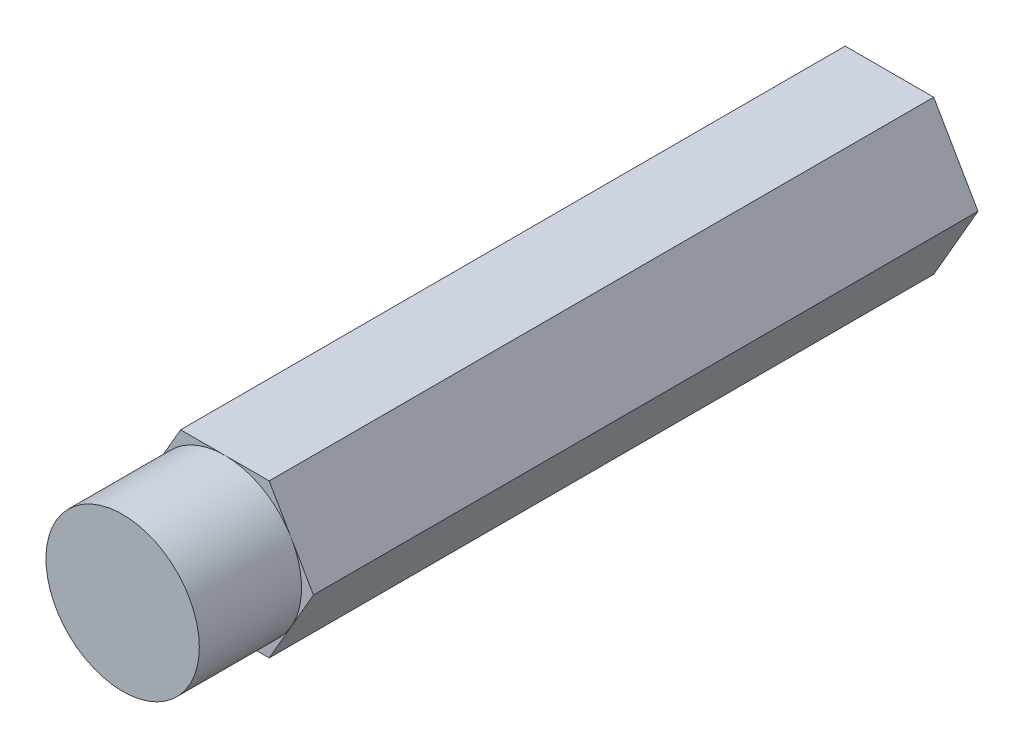
SolidWorks part; units mm, degrees
material "7075-T6 (SN)"
ref_plane "Front Plane" through (0, 0, 0) normal (0, 0, 1) x (1, 0, 0)
ref_plane "Top Plane" through (0, 0, 0) normal (0, 1, 0) x (1, 0, 0)
ref_plane "Right Plane" through (0, 0, 0) normal (1, 0, 0) x (0, 0, -1)
sketch "Sketch1" plane through (0, 0, 0) normal (0, 0, 1) x (1, 0, 0)
  line L1 (-2.7496, -4.7625) -> (2.7496, -4.7625)
  line L2 (2.7496, -4.7625) -> (5.4993, 0)
  line L3 (5.4993, 0) -> (2.7496, 4.7625)
  line L4 (2.7496, 4.7625) -> (-2.7496, 4.7625)
  line L5 (-2.7496, 4.7625) -> (-5.4993, 0)
  line L6 (-5.4993, 0) -> (-2.7496, -4.7625)
  circle A0 centre (0, 0) radius 4.7625 construction
  dimension "D1" = 9.525
extrude "Boss-Extrude1" add sketch "Sketch1" along normal blind 41.275
sketch "Sketch2" plane through (0, 0, 41.275) normal (0, 0, 1) x (1, 0, 0)
  circle A0 centre (0, 0) radius 4.7625
  dimension "D1" = 9.525
extrude "Boss-Extrude2" add sketch "Sketch2" along normal blind 6.35 contours A0
